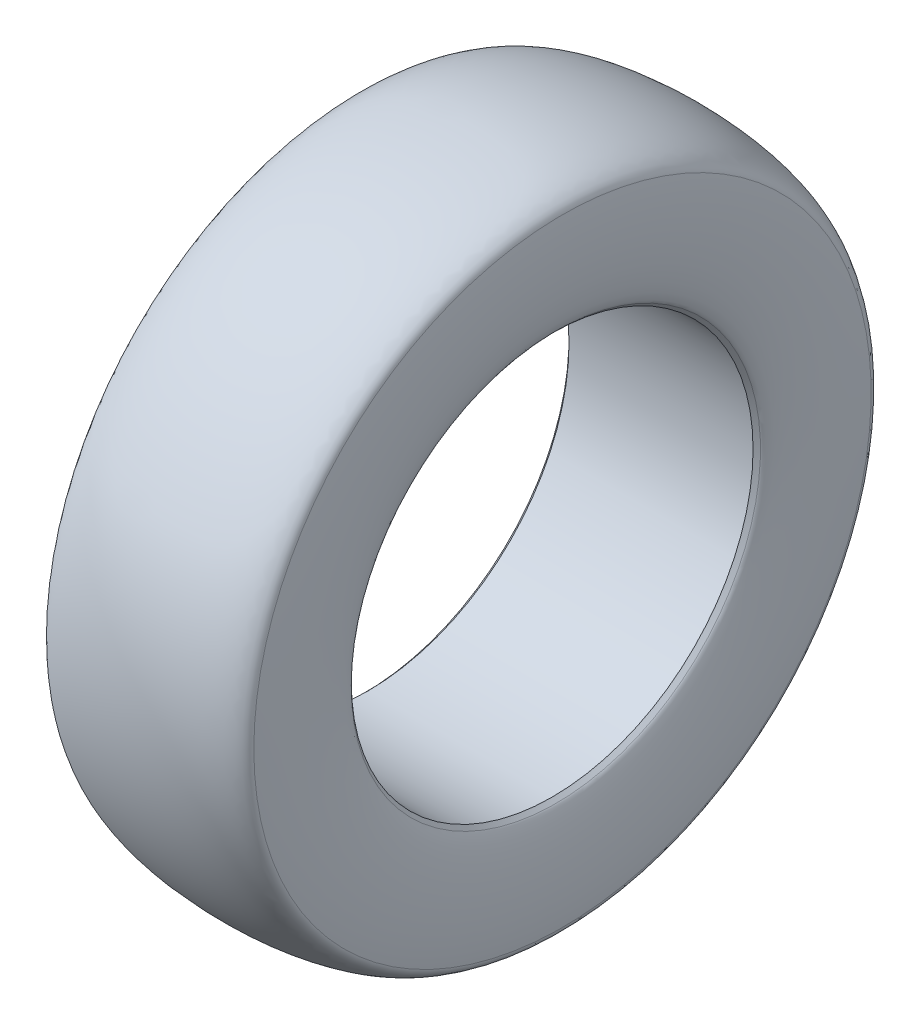
SolidWorks part; units mm, degrees
ref_plane "Front Plane" through (0, 0, 0) normal (0, 0, 1) x (1, 0, 0)
ref_plane "Top Plane" through (0, 0, 0) normal (0, 1, 0) x (1, 0, 0)
ref_plane "Right Plane" through (0, 0, 0) normal (1, 0, 0) x (0, 0, -1)
sketch "Sketch1" plane through (0, 0, 0) normal (0, 0, 1) x (1, 0, 0)
  line L0 (-1000, 0) -> (49000, 0) construction
  line L1 (-111.6697, 243.84) -> (111.6697, 243.84)
  line L2 (-127, 937.9425) -> (-127, -740.7419) construction
  line L3 (127, 852.2954) -> (127, -946.2951) construction
  line L4 (-682.5162, 406.4) -> (891.0312, 406.4) construction
  line L5 (-111.6697, 243.84) -> (-116.1599, 248.3301)
  line L6 (116.1599, 248.3301) -> (111.6697, 243.84)
  line L7 (0, 358.7485) -> (0, 466.2794) construction
  arc A0 (-116.1599, 248.3301) -> (-127, 243.84) centre (-120.65, 243.84) ccw construction
  arc A1 (127, 243.84) -> (116.1599, 248.3301) centre (120.65, 243.84) ccw construction
  ellipse E0 centre (-114.0568, 325.8863) end of major axis (-114.0568, 404.4869) minor radius 12.9432 (-124.217, 374.5807) -> (-116.1599, 248.3301) ccw
  ellipse E1 centre (0, 373.4459) end of major axis (-124.2907, 373.4459) minor radius 32.9541 (124.217, 374.5807) -> (-124.217, 374.5807) ccw
  ellipse E2 centre (114.0568, 325.8863) end of major axis (114.0568, 404.4869) minor radius 12.9432 (124.217, 374.5807) -> (116.1599, 248.3301) cw
  dimension "D4" = 12.7
  dimension "D2" = 254
  dimension "D3" = 406.4
revolve "Revolve1" add sketch "Sketch1" angle 360 about L0
